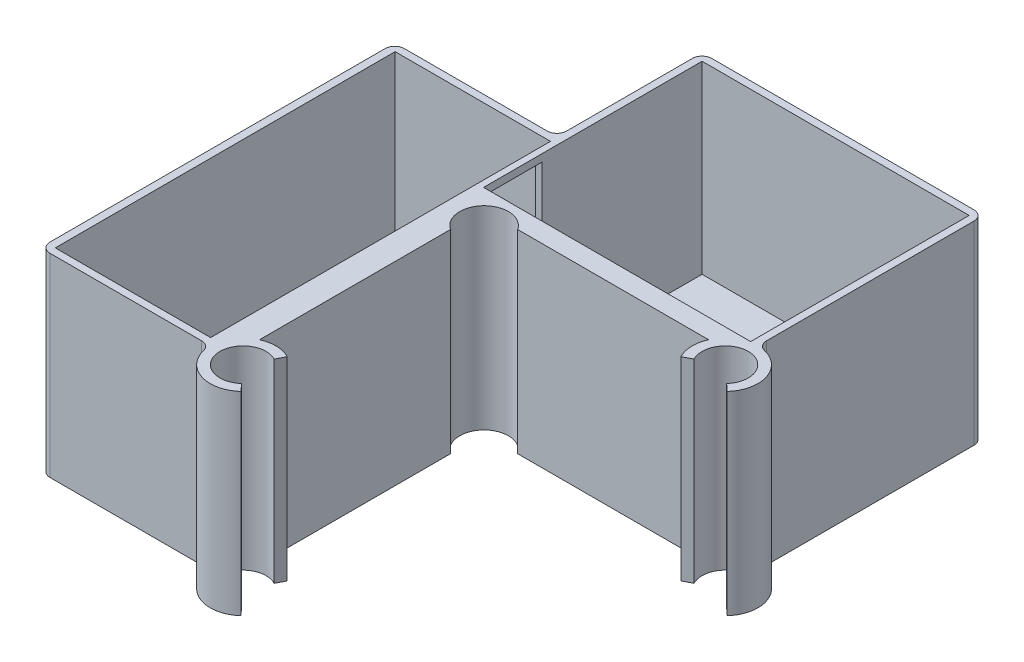
SolidWorks part; units mm, degrees
ref_plane "Front Plane" through (0, 0, 0) normal (0, 0, 1) x (1, 0, 0)
ref_plane "Top Plane" through (0, 0, 0) normal (0, 1, 0) x (1, 0, 0)
ref_plane "Right Plane" through (0, 0, 0) normal (1, 0, 0) x (0, 0, -1)
sketch "Sketch1" plane through (0, 0, 0) normal (0, 1, 0) x (1, 0, 0)
  line L0 (38.1377, -1.7345) -> (-11.5123, -1.7345)
  line L1 (41.6433, -11.6897) -> (43.1194, -13.0392)
  line L2 (38.1036, -8.4845) -> (45.1567, -8.4845) construction
  line L3 (38.1377, -8.4652) -> (38.1377, -5.3949) construction
  line L4 (33.9287, -10.686) -> (32.1564, -11.613)
  line L5 (31.9733, -5.7345) -> (-7.3365, -5.7345)
  line L6 (-11.5123, -8.4845) -> (-34.6522, 14.6553) construction
  line L7 (-9.3108, -53.9255) -> (-8.3838, -52.1533)
  line L8 (-8.3072, -61.6401) -> (-6.9576, -63.1162)
  line L9 (-18.2623, -58.1345) -> (-18.2623, -8.4845)
  line L10 (-14.2623, -51.9701) -> (-14.2623, -12.6603)
  arc A0 (33.9287, -10.686) -> (41.6433, -11.6897) centre (38.1377, -8.4845) cw
  arc A1 (43.1194, -13.0392) -> (38.1377, -1.7345) centre (38.1377, -8.4845) ccw
  arc A2 (32.1564, -11.613) -> (31.9733, -5.7345) centre (38.1377, -8.4845) cw
  arc A3 (-7.3365, -5.7345) -> (-14.2623, -12.6603) centre (-11.5123, -8.4845) ccw
  arc A4 (-11.5123, -1.7345) -> (-18.2623, -8.4845) centre (-11.5123, -8.4845) ccw
  arc A5 (-8.3838, -52.1533) -> (-14.2623, -51.9701) centre (-11.5123, -58.1345) ccw
  arc A6 (-9.3108, -53.9255) -> (-8.3072, -61.6401) centre (-11.5123, -58.1345) ccw
  arc A7 (-6.9576, -63.1162) -> (-18.2623, -58.1345) centre (-11.5123, -58.1345) cw
  dimension "D1" = 4.75
  dimension "D6" = 5
  dimension "D2" = 2
  dimension "D3" = 2
  dimension "D4" = 4
  dimension "D5" = 49.65
  dimension "D7" = 45
extrude "Boss-Extrude1" add sketch "Sketch1" along normal blind 40
sketch "Sketch8" plane through (0, 0, 0) normal (0, 1, 0) x (1, 0, 0)
  line L0 (38.1377, -1.7345) -> (38.1377, 44.7655)
  line L1 (38.1377, 44.7655) -> (-19.8623, 44.7655)
  line L2 (-19.8623, 44.7655) -> (-19.8623, 14.8655)
  line L3 (-19.8623, 14.8655) -> (-53.2623, 14.8655)
  line L4 (-53.2623, 14.8655) -> (-53.2623, -58.1345)
  line L5 (-53.2623, -58.1345) -> (-18.2623, -58.1345)
  line L6 (-18.2623, -58.1345) -> (-18.2623, -8.4845)
  line L7 (38.1377, -1.7345) -> (-11.5123, -1.7345)
  line L23 (-18.2623, -56.6345) -> (-18.2623, -8.4845)
  line L24 (36.6377, -1.7345) -> (-11.5123, -1.7345)
  arc A0 (-18.2623, -8.4845) -> (-11.5123, -1.7345) centre (-11.5123, -8.4845) cw
  arc A1 (-11.5123, -1.7345) -> (-18.2623, -8.4845) centre (-11.5123, -8.4845) ccw
  dimension "D1" = 46.5
  dimension "D2" = 58
  dimension "D3" = 73
  dimension "D4" = 35
extrude "Boss-Extrude6" add sketch "Sketch8" along normal blind 40 contours L6 A0 L7 L0 L1 L2 L3 L4 L5
sketch "Sketch9" plane through (0, 0, 0) normal (0, 1, 0) x (1, 0, 0)
  line L0 (38.1377, -1.7345) -> (38.1377, 44.7655) construction
  line L1 (36.6377, 43.2655) -> (-18.3623, 43.2655)
  line L2 (36.6377, 43.2655) -> (36.6377, -1.7345)
  line L3 (36.6377, -1.7345) -> (-18.3623, -1.7345)
  line L4 (-18.3623, 43.2655) -> (-18.3623, -1.7345)
  line L5 (38.1377, 44.7655) -> (-19.8623, 44.7655) construction
  dimension "D1" = 1.5
  dimension "D2" = 55
  dimension "D3" = 1.5
  dimension "D4" = 45
extrude "Cut-Extrude1" cut sketch "Sketch9" against normal blind 38 from surface at 40 starting at face at (0.8671, 40, 18.0745)
sketch "Sketch10" plane through (0, 0, 0) normal (0, 1, 0) x (1, 0, 0)
  line L0 (-53.2623, -58.1345) -> (-18.2623, -58.1345) construction
  line L1 (-51.6819, -56.6345) -> (-19.6819, -56.6345)
  line L2 (-51.6819, -56.6345) -> (-51.6819, 13.3655)
  line L3 (-51.6819, 13.3655) -> (-19.6819, 13.3655)
  line L4 (-19.6819, -56.6345) -> (-19.6819, 13.3655)
  line L5 (-53.2623, 14.8655) -> (-53.2623, -58.1345) construction
  dimension "D1" = 1.5
  dimension "D2" = 1.5805
  dimension "D3" = 32
  dimension "D4" = 70
extrude "Cut-Extrude3" cut sketch "Sketch10" against normal blind 38 from surface at 40 starting at face at (9.1377, 40, -20.7655)
fillet "Fillet4" radius 2 7 edges at (-19.8623, 20, -14.8655) (-18.2623, 20, 58.1345) (38.1377, 20, 1.7345) (38.1377, 20, -44.7655) (-19.8623, 20, -44.7655) (-53.2623, 20, 58.1345) (-53.2623, 20, -14.8655)
sketch "Sketch11" plane through (-18.3623, 0, 0) normal (1, 0, 0) x (0, 0, -1)
  line L0 (43.2655, 40) -> (-1.7345, 40) construction
  line L1 (-1.7345, 38.5) -> (10.2655, 38.5)
  line L2 (-1.7345, 38.5) -> (-1.7345, 2)
  line L3 (-1.7345, 2) -> (10.2655, 2)
  line L4 (10.2655, 38.5) -> (10.2655, 2)
  line L5 (43.2655, 0) -> (-1.7345, 0) construction
  line L6 (-1.7345, 2) -> (-1.7345, 40) construction
  dimension "D1" = 1.5
  dimension "D2" = 2
  dimension "D3" = 12
extrude "Cut-Extrude4" cut sketch "Sketch11" against normal blind 5
